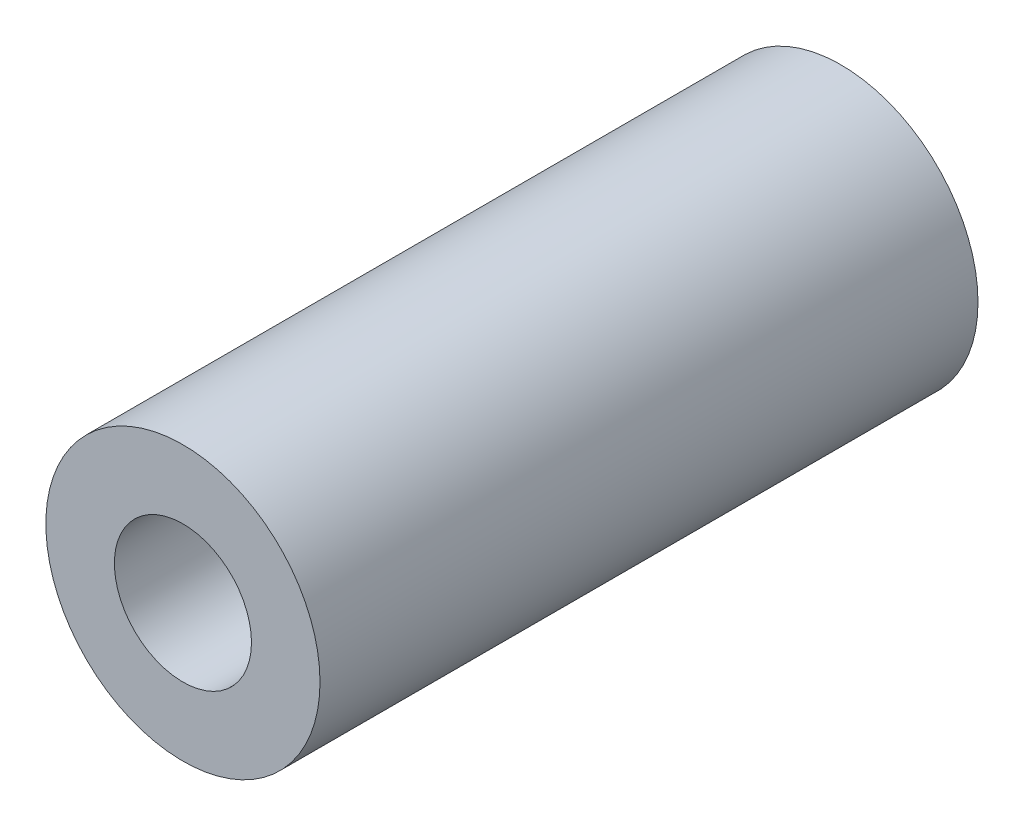
SolidWorks part; units mm, degrees
material "6061 合金"
ref_plane "前视基准面" through (0, 0, 0) normal (0, 0, 1) x (1, 0, 0)
ref_plane "上视基准面" through (0, 0, 0) normal (0, 1, 0) x (1, 0, 0)
ref_plane "右视基准面" through (0, 0, 0) normal (1, 0, 0) x (0, 0, -1)
sketch "草图1" plane through (0, 0, 0) normal (0, 0, 1) x (1, 0, 0)
  circle A1 centre (0, 0) radius 2.5
  dimension "D1" = 5
extrude "凸台-拉伸1" add sketch "草图1" along normal blind 12
hole_wizard "M3 螺纹孔1" positions "草图2" profile "草图3" tap size "M3" standard "GB" end condition through all
sketch "草图2" plane through (0, 0, 12) normal (0, 0, 1) x (1, 0, 0)
  point P0 (0, 0)
sketch "草图3" plane through (0, 0, 12) normal (1, 0, 0) x (0, -1, 0)
  line L0 (0, 0) -> (0, 12)
  line L1 (0, 12) -> (1.25, 12)
  line L2 (1.25, 12) -> (1.25, 0)
  line L5 (1.25, 0) -> (0, 0)
  line L11 (0, -6.35) -> (0, 107.95) construction
  dimension "通孔螺纹孔钻头直径" = 2.5
  dimension "通孔螺纹孔钻头深度" = 12
cosmetic thread "孔螺蚊线1"
